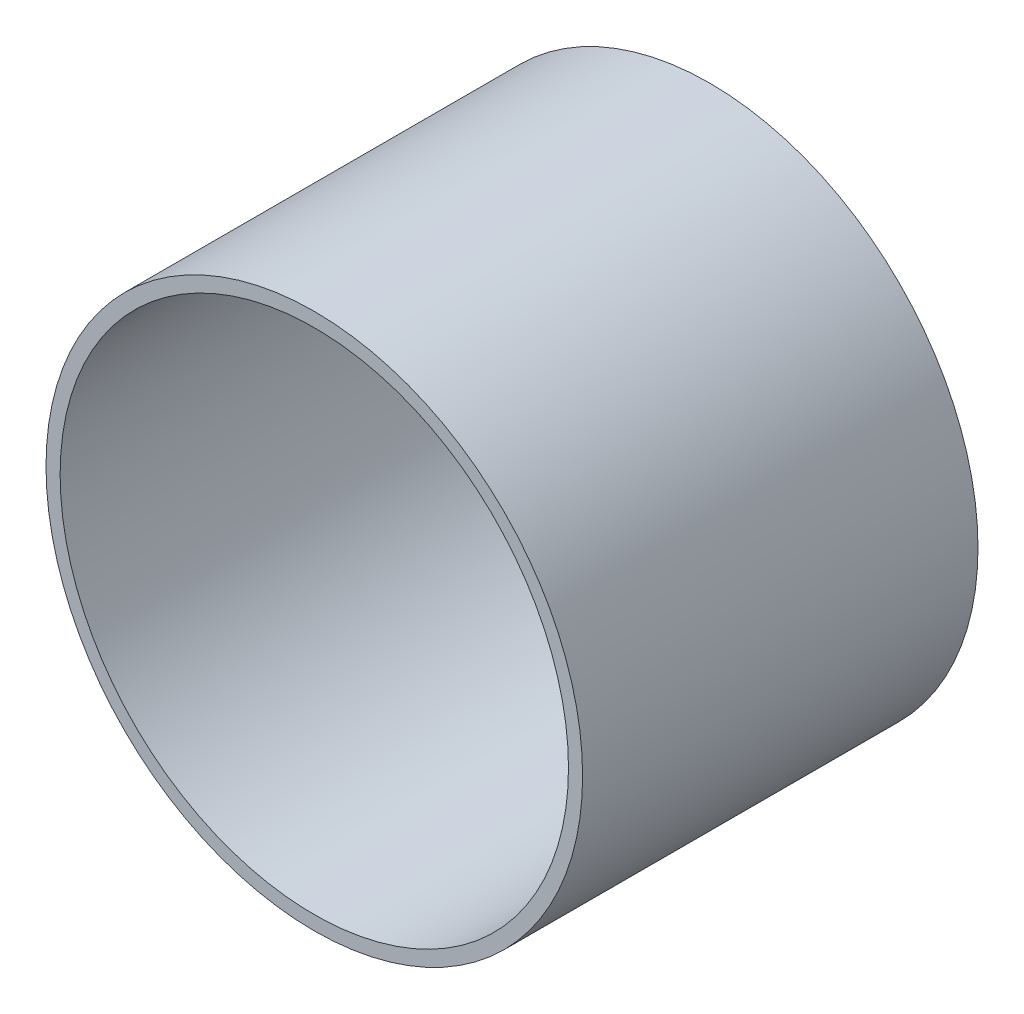
SolidWorks part; units mm, degrees
ref_plane "Front Plane" through (0, 0, 0) normal (0, 0, 1) x (1, 0, 0)
ref_plane "Top Plane" through (0, 0, 0) normal (0, 1, 0) x (1, 0, 0)
ref_plane "Right Plane" through (0, 0, 0) normal (1, 0, 0) x (0, 0, -1)
sketch "Sketch1" plane through (0, 0, 0) normal (0, 0, 1) x (1, 0, 0)
  circle A0 centre (0, 0) radius 9.5
  dimension "D1" = 19
extrude "Boss-Extrude1" add sketch "Sketch1" along normal blind 14
sketch "Sketch2" plane through (0, 0, 14) normal (0, 0, 1) x (1, 0, 0)
  circle A0 centre (0, 0) radius 9
  dimension "D1" = 18
extrude "Cut-Extrude1" cut sketch "Sketch2" against normal blind 13
